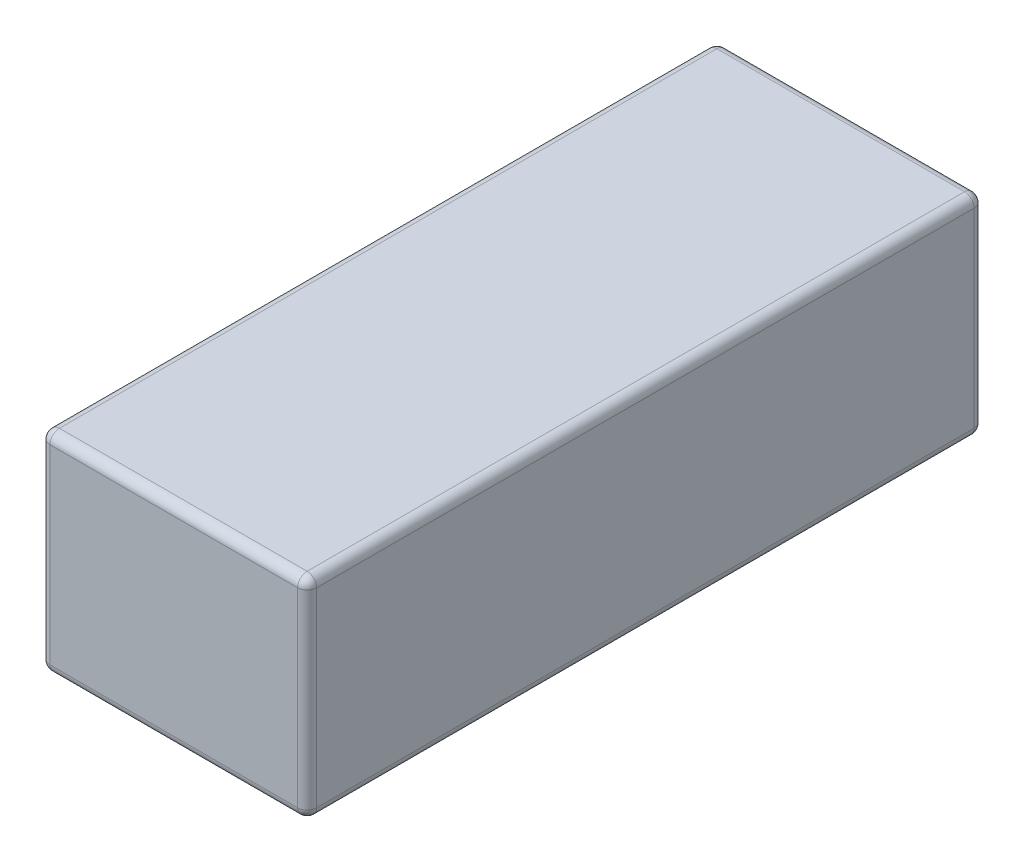
SolidWorks part; units mm, degrees
ref_plane "前视基准面" through (0, 0, 0) normal (0, 0, 1) x (1, 0, 0)
ref_plane "上视基准面" through (0, 0, 0) normal (0, 1, 0) x (1, 0, 0)
ref_plane "右视基准面" through (0, 0, 0) normal (1, 0, 0) x (0, 0, -1)
sketch "草图1" plane through (0, 0, 0) normal (0, 0, 1) x (1, 0, 0)
  line L1 (-28, 22) -> (28, 22)
  line L2 (-28, 22) -> (-28, -22)
  line L3 (-28, -22) -> (28, -22)
  line L4 (28, 22) -> (28, -22)
  line L5 (-28, 22) -> (28, -22) construction
  line L6 (-28, -22) -> (28, 22) construction
  point P0 (0, 0)
  dimension "D1" = 56
  dimension "D2" = 44
extrude "凸台-拉伸1" add sketch "草图1" along normal blind 142
fillet "圆角1" radius 2 12 edges at (-28, 0, 0) (-28, -22, 71) (0, -22, 0) (0, -22, 142) (-28, 0, 142) (28, -22, 71) (28, 0, 142) (28, 0, 0) (28, 22, 71) (0, 22, 142) (-28, 22, 71) (0, 22, 0)
